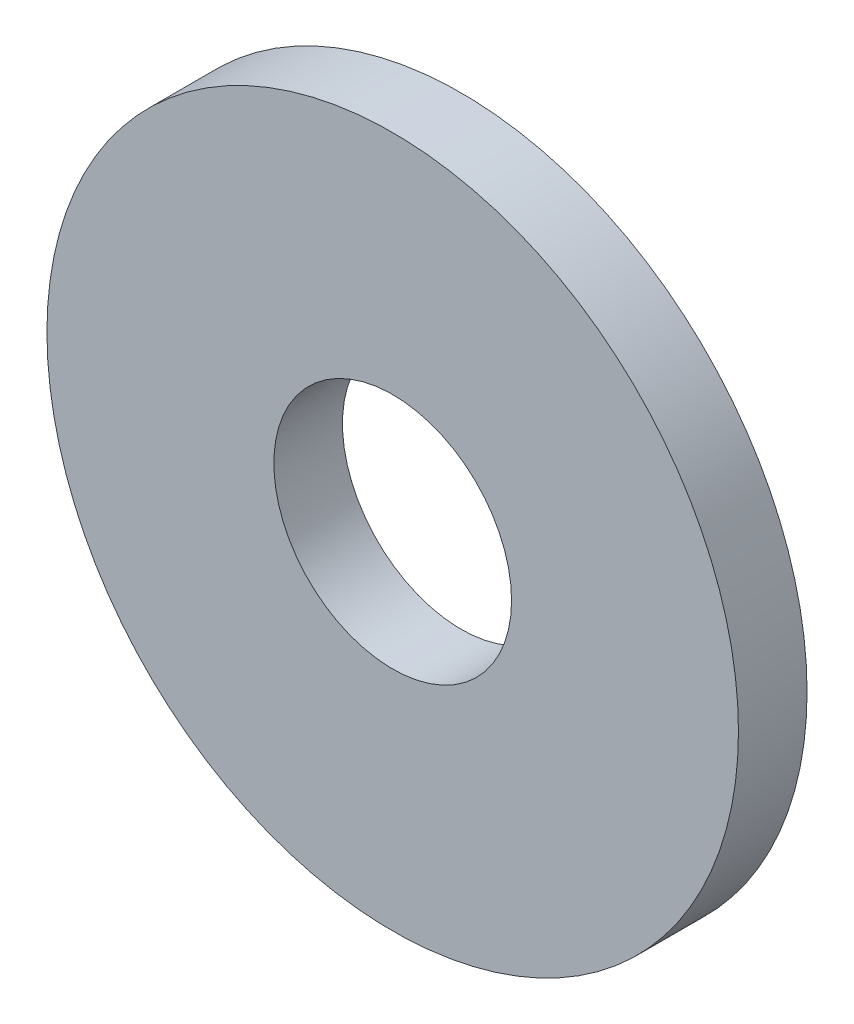
SolidWorks part; units mm, degrees
material "Delrin 2700 NC010, Low Viscosity Acetal Copolymer (SS)"
ref_plane "Front Plane" through (0, 0, 0) normal (0, 0, 1) x (1, 0, 0)
ref_plane "Top Plane" through (0, 0, 0) normal (0, 1, 0) x (1, 0, 0)
ref_plane "Right Plane" through (0, 0, 0) normal (1, 0, 0) x (0, 0, -1)
sketch "Sketch1" plane through (0, 0, 0) normal (0, 0, 1) x (1, 0, 0)
  circle A0 centre (0, 0) radius 11
  circle A1 centre (0, 0) radius 32
  dimension "D1" = 22
  dimension "D2" = 64
extrude "Boss-Extrude1" add sketch "Sketch1" along normal blind 6.35
